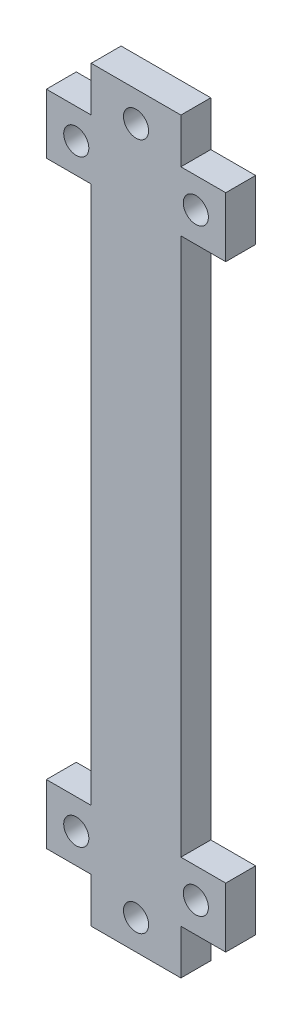
SolidWorks part; units mm, degrees
ref_plane "Front Plane" through (0, 0, 0) normal (0, 0, 1) x (1, 0, 0)
ref_plane "Top Plane" through (0, 0, 0) normal (0, 1, 0) x (1, 0, 0)
ref_plane "Right Plane" through (0, 0, 0) normal (1, 0, 0) x (0, 0, -1)
sketch "Sketch1" plane through (0, 0, 0) normal (0, 0, 1) x (1, 0, 0)
  line L0 (15, 45) -> (50.9125, 45) construction
  line L1 (0, 0) -> (15, 0)
  line L2 (0, 0) -> (0, 90)
  line L3 (0, 90) -> (15, 90)
  line L4 (15, 0) -> (15, 90)
  line L5 (-7.5, 90) -> (22.5, 90)
  line L6 (-7.5, 90) -> (-7.5, 100)
  line L7 (-7.5, 100) -> (22.5, 100)
  line L8 (22.5, 90) -> (22.5, 100)
  line L9 (22.5, 0) -> (22.5, -10)
  line L10 (-7.5, -10) -> (22.5, -10)
  line L11 (-7.5, 0) -> (-7.5, -10)
  line L12 (-7.5, 0) -> (22.5, 0)
  line L13 (0, 0) -> (15, 0)
  line L14 (7.5, 100) -> (7.5, 96.9081) construction
  line L15 (0, -17.5) -> (15, -17.5)
  line L16 (0, 100) -> (15, 100)
  line L17 (0, 100) -> (0, 107.5)
  line L18 (0, 107.5) -> (15, 107.5)
  line L19 (15, 100) -> (15, 107.5)
  line L20 (15, -10) -> (15, -17.5)
  line L21 (0, -10) -> (15, -10)
  line L22 (0, -10) -> (0, -17.5)
  line L23 (7.5, -10) -> (7.5, -6.9081) construction
  circle A0 centre (-2.5, 95) radius 2.1
  circle A1 centre (17.5, 95) radius 2.1
  circle A2 centre (-2.5, -5) radius 2.1
  circle A3 centre (17.5, -5) radius 2.1
  circle A4 centre (7.5, 102.5) radius 2.1
  circle A5 centre (7.5, -12.5) radius 2.1
  point P9 (7.5, 100)
  point P10 (7.5, 0)
  point P20 (-7.5, 95)
  point P32 (7.5, 107.5)
  point P35 (0, 0)
  point P36 (0, 0)
  point P37 (0, 0)
  dimension "D5" = 4.2
  dimension "D6" = 5
  dimension "D9" = 4.2
  dimension "D10" = 2.5
  dimension "D1" = 90
  dimension "D2" = 15
  dimension "D3" = 30
  dimension "D4" = 10
  dimension "D7" = 7.5
  dimension "D8" = 15
extrude "Boss-Extrude1" add sketch "Sketch1" along normal blind 5 contours L1 L4 L3 L2 | L5 L8 L7 L6 L3 A0 A1 | L7 L19 L18 L17 A4 | L12 L11 L10 L9 L1 A3 A2 | L10 L22 L15 L20 A5
